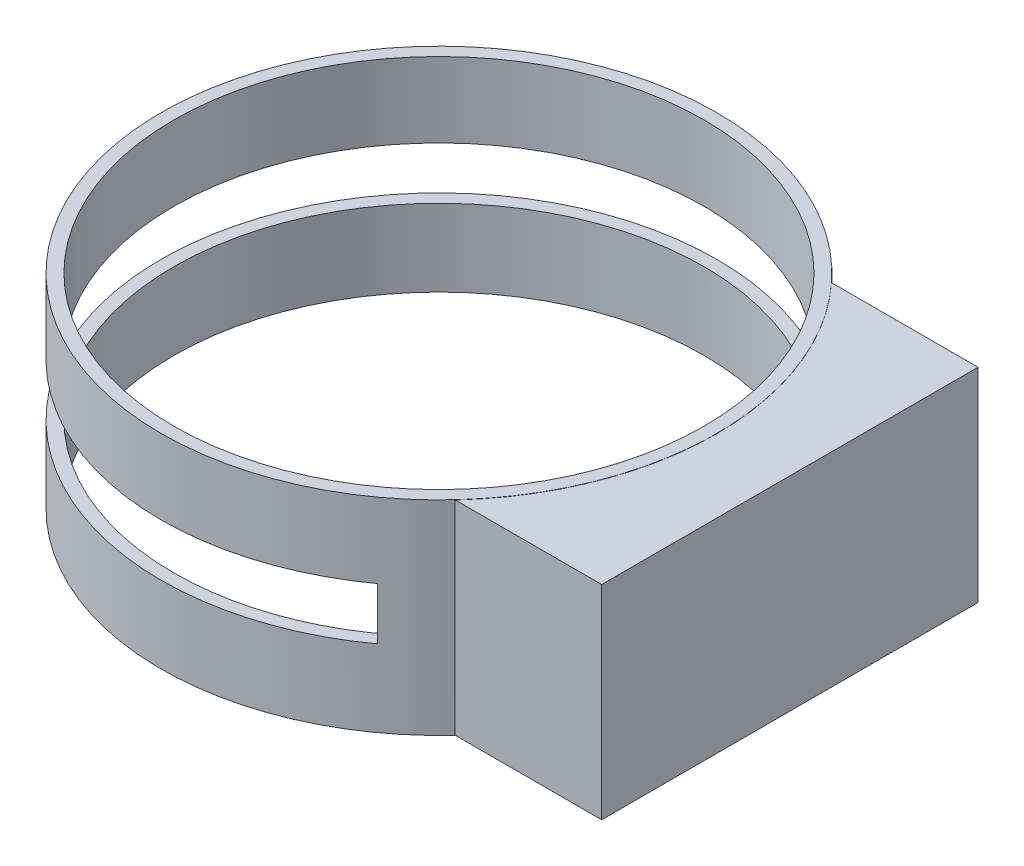
SolidWorks part; units mm, degrees
ref_plane "Alzado" through (0, 0, 0) normal (0, 0, 1) x (1, 0, 0)
ref_plane "Planta" through (0, 0, 0) normal (0, 1, 0) x (1, 0, 0)
ref_plane "Vista lateral" through (0, 0, 0) normal (1, 0, 0) x (0, 0, -1)
sketch "Croquis1" plane through (0, 0, 0) normal (0, 1, 0) x (1, 0, 0)
  circle A0 centre (0, 0) radius 65
  circle A1 centre (0, 0) radius 68.105
  dimension "D1" = 130
extrude "Saliente-Extruir1" add sketch "Croquis1" along normal blind 50
sketch "Croquis2" plane through (0, 0, 0) normal (1, 0, 0) x (0, 0, -1)
  line L0 (-68.105, 0) -> (68.105, 0) construction
  line L1 (-46.1199, 49.9447) -> (46.1199, 49.9447)
  line L2 (-46.1199, 49.9447) -> (-46.1199, 0)
  line L3 (-46.1199, 0) -> (46.1199, 0)
  line L4 (46.1199, 49.9447) -> (46.1199, 0)
  line L5 (-46.1199, 49.9447) -> (46.1199, 0) construction
  line L6 (-46.1199, 0) -> (46.1199, 49.9447) construction
  point P0 (0, 24.9723)
extrude "Saliente-Extruir2" add sketch "Croquis2" along normal blind 86
sketch "Croquis3" plane through (0, 50, 0) normal (0, 1, 0) x (1, 0, 0)
  circle A0 centre (0, 0) radius 65
extrude "Cortar-Extruir1" cut sketch "Croquis3" against normal blind 86
ref_plane "Plano1" through (40, 0, 0) normal (1, 0, 0) x (0, 0, -1)
sketch "Croquis4" plane through (40, 0, 0) normal (1, 0, 0) x (0, 0, -1)
  line L1 (77.0734, 31.6496) -> (-82.3046, 31.6496)
  line L2 (77.0734, 31.6496) -> (77.0734, 18.8522)
  line L3 (77.0734, 18.8522) -> (-82.3046, 18.8522)
  line L4 (-82.3046, 31.6496) -> (-82.3046, 18.8522)
  line L5 (77.0734, 31.6496) -> (-82.3046, 18.8522) construction
  line L6 (77.0734, 18.8522) -> (-82.3046, 31.6496) construction
  point P0 (-2.6156, 25.2509)
  point P5 (-78.2898, 31.6496)
  point P6 (-82.3046, 18.8522)
extrude "Cortar-Extruir2" cut sketch "Croquis4" against normal blind 144
ref_plane "Plano2" through (0, 0, 0) normal (0, 0, 1) x (1, 0, 0)
